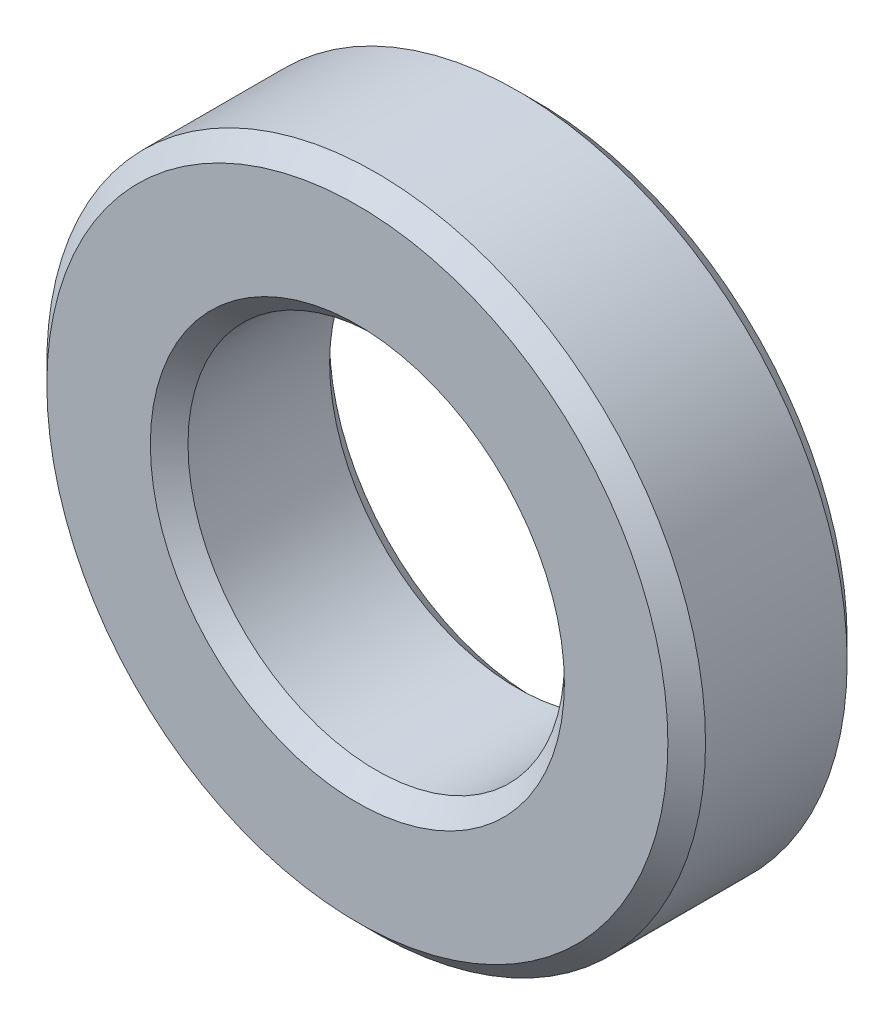
SolidWorks part; units mm, degrees
material "Latão"
ref_plane "Plano frontal" through (0, 0, 0) normal (0, 0, 1) x (1, 0, 0)
ref_plane "Plano superior" through (0, 0, 0) normal (0, 1, 0) x (1, 0, 0)
ref_plane "Plano direito" through (0, 0, 0) normal (1, 0, 0) x (0, 0, -1)
sketch "Esboço1" plane through (0, 0, 0) normal (0, 0, 1) x (1, 0, 0)
  circle A0 centre (0, 0) radius 17.5
  circle A1 centre (0, 0) radius 10
  dimension "D1" = 35
  dimension "D2" = 20
extrude "Ressalto-extrusão1" add sketch "Esboço1" along normal blind 9.525
chamfer "Chanfro1" distance 1 angle 45 4 edges at (10, 0, 9.525) (10, 0, 0) (17.5, 0, 0) (17.5, 0, 9.525)
